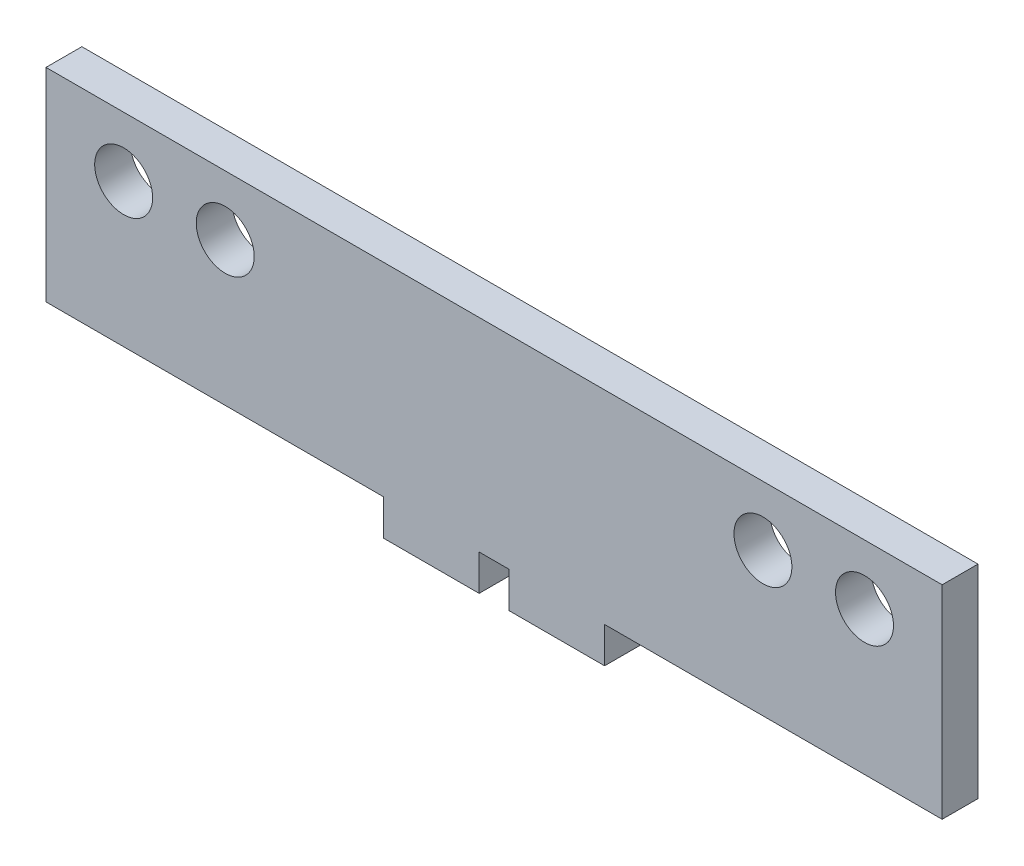
SolidWorks part; units mm, degrees
ref_plane "Front Plane" through (0, 0, 0) normal (0, 0, 1) x (1, 0, 0)
ref_plane "Top Plane" through (0, 0, 0) normal (0, 1, 0) x (1, 0, 0)
ref_plane "Right Plane" through (0, 0, 0) normal (1, 0, 0) x (0, 0, -1)
sketch "Sketch1" plane through (0, 0, 0) normal (0, 0, 1) x (1, 0, 0)
  line L1 (-37.5, 8.5) -> (37.5, 8.5)
  line L2 (-37.5, 8.5) -> (-37.5, -8.5)
  line L3 (-37.5, -8.5) -> (37.5, -8.5)
  line L4 (37.5, 8.5) -> (37.5, -8.5)
  point P0 (0, 0)
  dimension "D1" = 75
  dimension "D2" = 17
extrude "Boss-Extrude1" add sketch "Sketch1" along normal blind 3
sketch "Sketch2" plane through (0, -8.5, 0) normal (0, -1, 0) x (-1, 0, 0)
  line L0 (37.5, -3) -> (-37.5, -3) construction
  line L1 (9.25, -3) -> (1.25, -3)
  line L2 (9.25, -3) -> (9.25, 0)
  line L3 (9.25, 0) -> (1.25, 0)
  line L4 (1.25, -3) -> (1.25, 0)
  line L5 (37.5, 0) -> (-37.5, 0) construction
  line L6 (37.5, -3) -> (37.5, 0) construction
  line L7 (-9.25, -3) -> (-1.25, -3)
  line L8 (-9.25, -3) -> (-9.25, 0)
  line L9 (-9.25, 0) -> (-1.25, 0)
  line L10 (-1.25, -3) -> (-1.25, 0)
  line L11 (-37.5, -3) -> (-37.5, 0) construction
  dimension "D1" = 8
  dimension "D2" = 8
  dimension "D3" = 28.25
  dimension "D4" = 28.25
extrude "Boss-Extrude2" add sketch "Sketch2" along normal blind 3
sketch "Sketch3" plane through (0, 0, 3) normal (0, 0, 1) x (1, 0, 0)
  line L0 (-37.5, 8.5) -> (-37.5, -8.5) construction
  line L1 (37.5, 8.5) -> (-37.5, 8.5) construction
  line L2 (37.5, -8.5) -> (37.5, 8.5) construction
  circle A0 centre (-31, 3.5) radius 2.425
  circle A1 centre (-22.5, 3.5) radius 2.425
  circle A2 centre (22.5, 3.5) radius 2.425
  circle A3 centre (31, 3.5) radius 2.425
  dimension "D1" = 4.85
  dimension "D4" = 4.85
  dimension "D6" = 4.85
  dimension "D7" = 4.85
  dimension "D2" = 6.5
  dimension "D3" = 5
  dimension "D5" = 15
  dimension "D8" = 6.5
  dimension "D9" = 15
extrude "Cut-Extrude1" cut sketch "Sketch3" against normal blind 3
